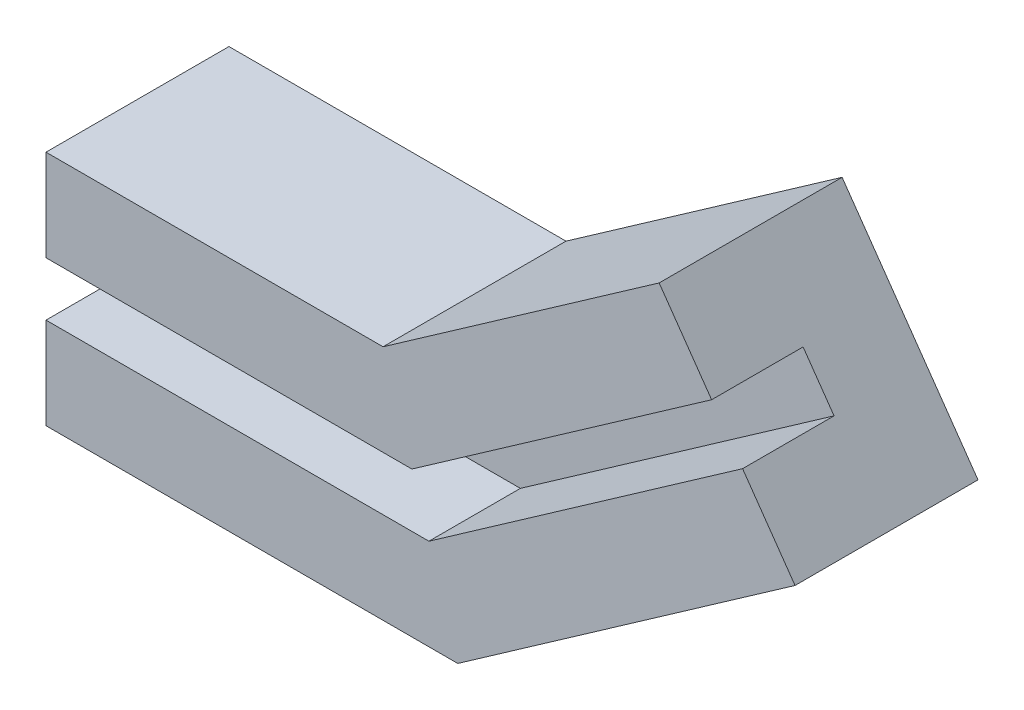
SolidWorks part; units mm, degrees
ref_plane "Ebene vorne" through (0, 0, 0) normal (0, 0, 1) x (1, 0, 0)
ref_plane "Ebene oben" through (0, 0, 0) normal (0, 1, 0) x (1, 0, 0)
ref_plane "Ebene rechts" through (0, 0, 0) normal (1, 0, 0) x (0, 0, -1)
sketch "Skizze1" plane through (0, 0, 0) normal (0, 0, 1) x (1, 0, 0)
  line L0 (0, 0) -> (31.8603, 0)
  line L1 (31.8603, 0) -> (57.9587, 18.2743)
  line L2 (57.9587, 18.2743) -> (54.5746, 23.1073)
  line L3 (54.5746, 23.1073) -> (30, 5.9)
  line L4 (30, 5.9) -> (0, 5.9)
  line L5 (0, 5.9) -> (0, 0)
  line L6 (26.847, 15.9) -> (-10, 15.9)
  line L7 (-10, 15.9) -> (-10, -10)
  line L8 (-10, -10) -> (35.0133, -10)
  line L9 (35.0133, -10) -> (71.8859, 15.8185)
  line L10 (71.8859, 15.8185) -> (57.0303, 37.0346)
  line L11 (57.0303, 37.0346) -> (26.847, 15.9)
  line L12 (0, 5.9) -> (-10, 5.9)
  line L13 (0, 0) -> (-10, 0)
  line L14 (54.5746, 23.1073) -> (62.7661, 28.8431)
  line L15 (57.9587, 18.2743) -> (66.1502, 24.0101)
  dimension "D1" = 145
  dimension "D2" = 30
  dimension "D3" = 5.9
  dimension "D4" = 10
extrude "Aufsatz-Linear austragen2" add sketch "Skizze1" along normal blind 10 contours L3 L14 L10 L11 L6 L7 L12 L4 | L15 L1 L0 L13 L7 L8 L9 L10
sketch "Skizze2" plane through (0, 0, 0) normal (0, 0, -1) x (-1, 0, 0)
  line L0 (-57.0303, 37.0346) -> (-26.847, 15.9)
  line L5 (-26.847, 15.9) -> (-35.0133, -10)
  line L6 (-71.8859, 15.8185) -> (-57.0303, 37.0346)
  line L7 (-35.0133, -10) -> (-71.8859, 15.8185)
  line L8 (-26.847, 15.9) -> (10, 15.9)
  line L9 (10, 15.9) -> (10, -10)
  line L10 (10, -10) -> (-35.0133, -10)
  line L11 (-26.847, 15.9) -> (-35.0133, -10)
  line M5 (-62.7661, 28.8431) -> (-30, 5.9)
  line M6 (-30, 5.9) -> (10, 5.9)
  line M7 (10, 5.9) -> (10, 15.9)
  line M8 (10, 15.9) -> (-26.847, 15.9)
  line M9 (-26.847, 15.9) -> (-57.0303, 37.0346)
  line M10 (-57.0303, 37.0346) -> (-62.7661, 28.8431)
extrude "Aufsatz-Linear austragen3" add sketch "Skizze2" along normal blind 10 contours L5 M8 M6 M7 | L10 L9 L5 M6 | L7 L5 L6 M5 | L5 M9 M10 M5
